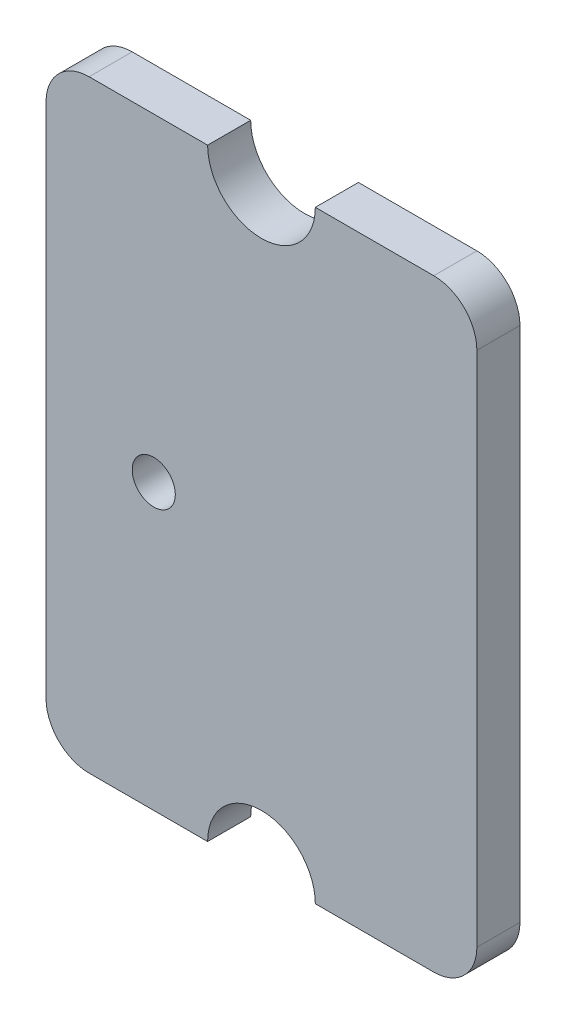
SolidWorks part; units mm, degrees
ref_plane "Plan de face" through (0, 0, 0) normal (0, 0, 1) x (1, 0, 0)
ref_plane "Plan de dessus" through (0, 0, 0) normal (0, 1, 0) x (1, 0, 0)
ref_plane "Plan de droite" through (0, 0, 0) normal (1, 0, 0) x (0, 0, -1)
sketch "Esquisse1" plane through (0, 0, 0) normal (0, 0, 1) x (1, 0, 0)
  line L0 (1.25, 7) -> (4, 7)
  line L1 (-4, 7) -> (-1.25, 7)
  line L2 (-5, 6) -> (-5, -6)
  line L3 (-4, -7) -> (-1.25, -7)
  line L4 (5, 6) -> (5, -6)
  line L5 (-5, 7) -> (5, -7) construction
  line L6 (-5, -7) -> (5, 7) construction
  line L7 (1.25, -7) -> (4, -7)
  arc A0 (4, 7) -> (5, 6) centre (4, 6) cw
  arc A1 (4, -7) -> (5, -6) centre (4, -6) ccw
  arc A2 (-5, -6) -> (-4, -7) centre (-4, -6) ccw
  arc A3 (-4, 7) -> (-5, 6) centre (-4, 6) ccw
  arc A4 (-1.25, 7) -> (1.25, 7) centre (0, 7) ccw
  arc A5 (1.25, -7) -> (-1.25, -7) centre (0, -7) ccw
  circle A6 centre (-2.5, -0.4) radius 0.5
  point P0 (0, 0)
  dimension "D3" = 1
  dimension "D4" = 2.5
  dimension "D5" = 6.6
  dimension "D6" = 1
  dimension "D1" = 10
  dimension "D2" = 14
  dimension "D7" = 2.5
extrude "Boss.-Extru.1" add sketch "Esquisse1" along normal blind 1
